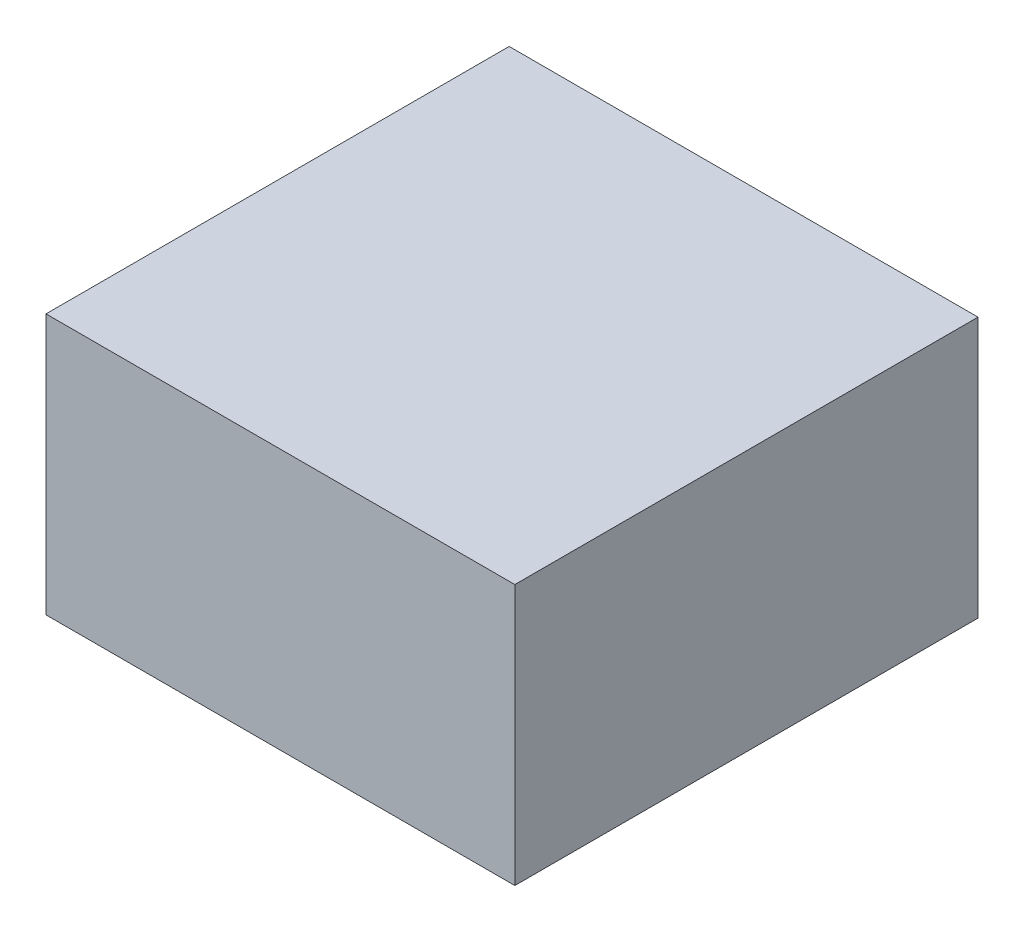
SolidWorks part; units mm, degrees
ref_plane "Front Plane" through (0, 0, 0) normal (0, 0, 1) x (1, 0, 0)
ref_plane "Top Plane" through (0, 0, 0) normal (0, 1, 0) x (1, 0, 0)
ref_plane "Right Plane" through (0, 0, 0) normal (1, 0, 0) x (0, 0, -1)
sketch "Sketch1" plane through (0, 0, 0) normal (0, 1, 0) x (1, 0, 0)
  line L0 (9, -15) -> (22.5, -15) construction
  line L1 (0, 93.6724) -> (110, 93.6724)
  line L2 (0, 93.6724) -> (0, -15)
  line L3 (0, -15) -> (110, -15)
  line L4 (110, 93.6724) -> (110, -15)
  line L5 (0, 87) -> (0, 0) construction
  line L6 (110, 0) -> (110, 87) construction
extrude "SCROD-and-carriers" add sketch "Sketch1" along normal up to surface (48.1652 mm away) and the other way up to surface (13 mm away)
